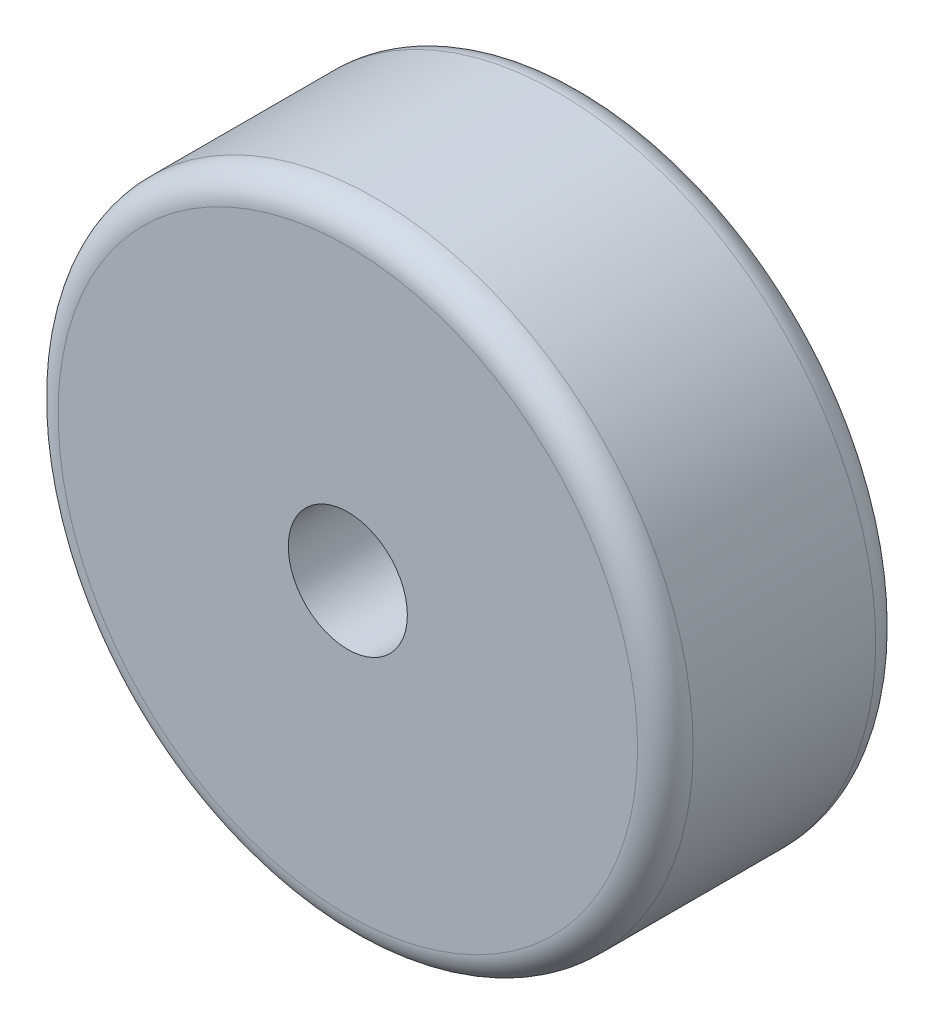
SolidWorks part; units mm, degrees
ref_plane "Front Plane" through (0, 0, 0) normal (0, 0, 1) x (1, 0, 0)
ref_plane "Top Plane" through (0, 0, 0) normal (0, 1, 0) x (1, 0, 0)
ref_plane "Right Plane" through (0, 0, 0) normal (1, 0, 0) x (0, 0, -1)
sketch "Sketch1" plane through (0, 0, 0) normal (0, 0, 1) x (1, 0, 0)
  circle A0 centre (0, 0) radius 19.05
  circle A1 centre (0, 0) radius 101.6
  dimension "D1" = 203.2
  dimension "D2" = 38.1
extrude "Boss-Extrude1" add sketch "Sketch1" along normal mid plane 76.2
fillet "Fillet1" radius 8.89 2 edges at (101.6, 0, -38.1) (101.6, 0, 38.1)
